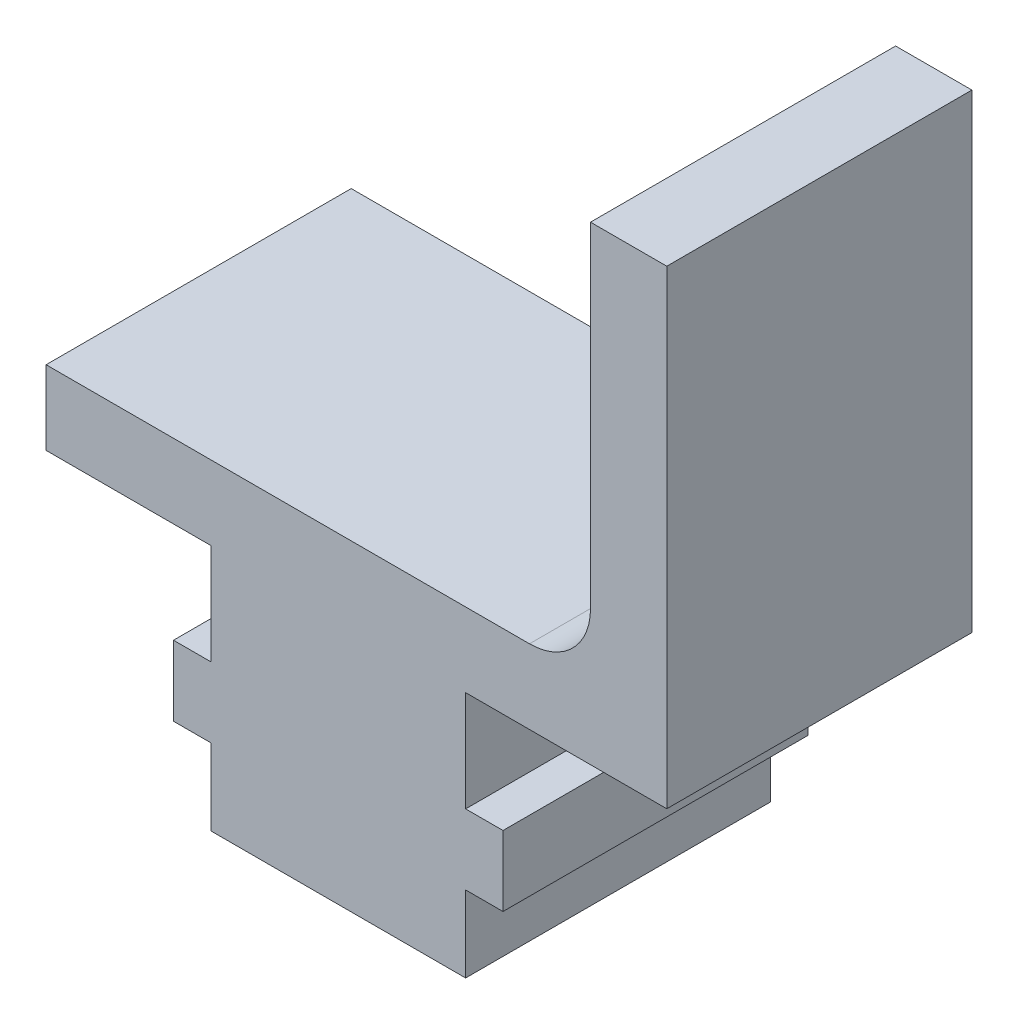
SolidWorks part; units mm, degrees
ref_plane "Front Plane" through (0, 0, 0) normal (0, 0, 1) x (1, 0, 0)
ref_plane "Top Plane" through (0, 0, 0) normal (0, 1, 0) x (1, 0, 0)
ref_plane "Right Plane" through (0, 0, 0) normal (1, 0, 0) x (0, 0, -1)
sketch "Sketch1" plane through (0, 0, 0) normal (0, 0, 1) x (1, 0, 0)
  line L0 (0, 0) -> (0, -4.191)
  line L1 (0, -4.191) -> (-1.5558, -4.191)
  line L2 (-1.5558, -4.191) -> (-1.5558, -7.112)
  line L3 (-1.5558, -7.112) -> (0, -7.112)
  line L4 (0, -7.112) -> (0, -10.287)
  line L5 (0, -10.287) -> (10.6045, -10.287)
  line L6 (10.6045, -10.287) -> (10.6045, -7.112)
  line L7 (10.6045, -7.112) -> (12.1603, -7.112)
  line L8 (12.1603, -7.112) -> (12.1603, -4.191)
  line L9 (12.1603, -4.191) -> (10.6045, -4.191)
  line L10 (10.6045, -4.191) -> (10.6045, 0)
  line L11 (10.6045, 0) -> (18.9772, 0)
  line L12 (18.9772, 0) -> (18.9772, 19.558)
  line L13 (18.9772, 19.558) -> (15.8022, 19.558)
  line L14 (15.8022, 19.558) -> (15.8022, 3.089)
  line L15 (15.8022, 3.089) -> (-6.858, 3.089)
  line L16 (-6.858, 3.089) -> (-6.858, 0)
  line L17 (-6.858, 0) -> (0, 0)
  line L18 (5.3022, -10.287) -> (5.3022, 13.589) construction
  circle A0 centre (5.3022, 13.589) radius 10.5 construction
  dimension "D9" = 21
  dimension "D1" = 10.6045
  dimension "D2" = 2.921
  dimension "D3" = 3.175
  dimension "D4" = 4.191
  dimension "D5" = 13.716
  dimension "D6" = 3.175
  dimension "D7" = 19.558
  dimension "D8" = 23.876
  dimension "D10" = 6.858
extrude "Boss-Extrude1" add sketch "Sketch1" along normal blind 12.7
fillet "Fillet1" radius 2.54 1 edges at (15.8022, 3.089, 6.35)
